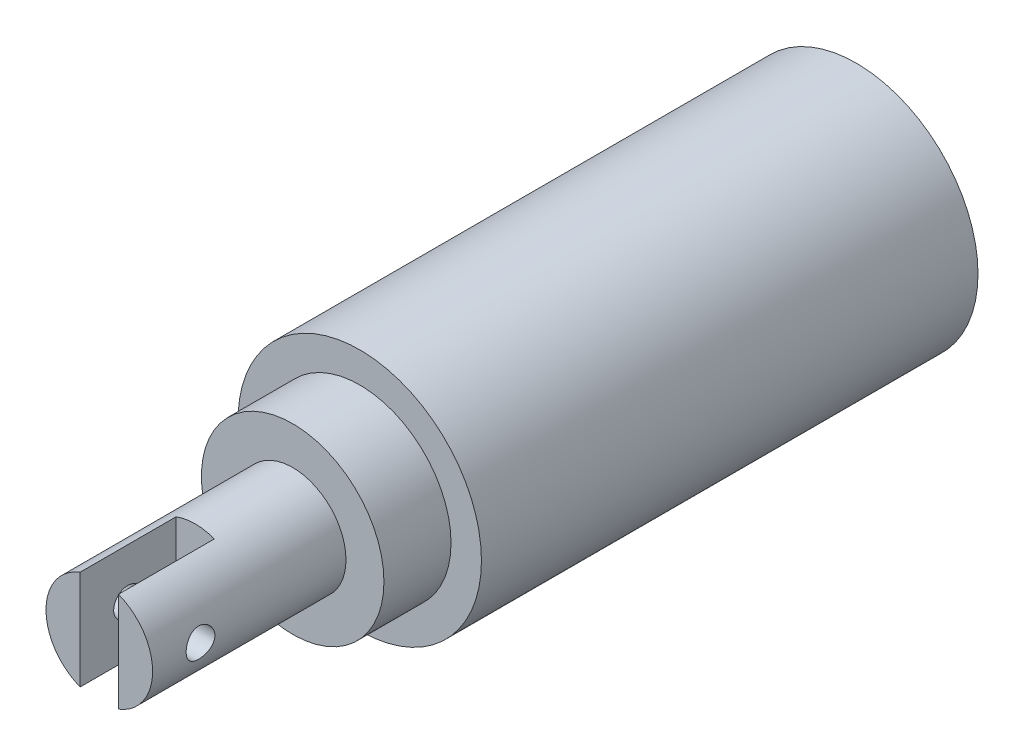
SolidWorks part; units mm, degrees
ref_plane "정면" through (0, 0, 0) normal (0, 0, 1) x (1, 0, 0)
ref_plane "윗면" through (0, 0, 0) normal (0, 1, 0) x (1, 0, 0)
ref_plane "우측면" through (0, 0, 0) normal (1, 0, 0) x (0, 0, -1)
sketch "Sketch1" plane through (0, 0, 0) normal (0, 0, 1) x (1, 0, 0)
  circle A0 centre (0, 0) radius 12.7
  dimension "D1" = 25.4
extrude "Extrude1" add sketch "Sketch1" along normal blind 51.816
sketch "Sketch2" plane through (0, 0, 51.816) normal (0, 0, 1) x (1, 0, 0)
  circle A0 centre (0, 0) radius 9.525
  dimension "D1" = 19.05
extrude "Extrude2" add sketch "Sketch2" along normal blind 7
sketch "Sketch3" plane through (0, 0, 58.816) normal (0, 0, 1) x (1, 0, 0)
  circle A0 centre (0, 0) radius 5.5626
  dimension "D1" = 11.1252
extrude "Extrude3" add sketch "Sketch3" along normal blind 20.178
sketch "Sketch4" plane through (0, 0, 78.994) normal (0, 0, 1) x (1, 0, 0)
  line L1 (2, 6) -> (-2, 6)
  line L2 (2, 6) -> (2, -6)
  line L3 (2, -6) -> (-2, -6)
  line L4 (-2, 6) -> (-2, -6)
  circle A0 centre (0, 0) radius 5.5626 construction
  dimension "D1" = 2
  dimension "D4" = 6
  dimension "D2" = 4
  dimension "D3" = 12
extrude "Cut-Extrude1" cut sketch "Sketch4" against normal blind 10
sketch "Sketch5" plane through (2, 0, 0) normal (-1, 0, 0) x (0, 0, 1)
  line L0 (68.994, 5.1906) -> (78.994, 5.1906) construction
  line L1 (78.994, -5.1906) -> (78.994, 5.1906) construction
  circle A0 centre (73.994, 0.0006) radius 1.5
  dimension "D1" = 3
  dimension "D2" = 5.19
  dimension "D3" = 5
extrude "Cut-Extrude2" cut sketch "Sketch5" against normal blind 10 and the other way blind 10
